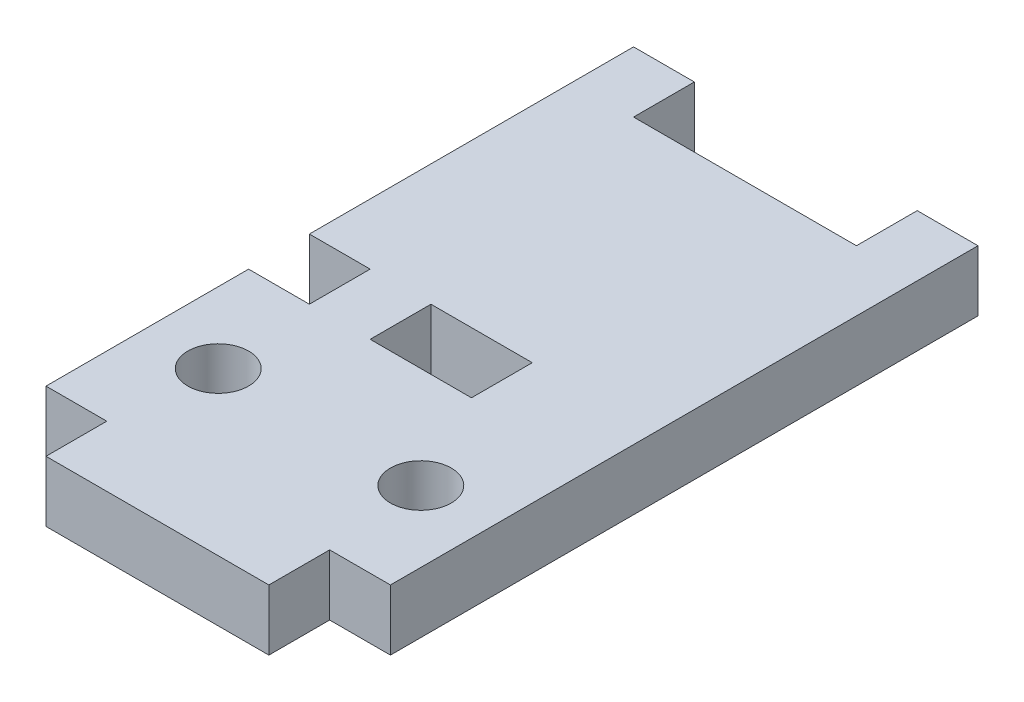
SolidWorks part; units mm, degrees
ref_plane "Plano frontal" through (0, 0, 0) normal (0, 0, 1) x (1, 0, 0)
ref_plane "Plano superior" through (0, 0, 0) normal (0, 1, 0) x (1, 0, 0)
ref_plane "Plano direito" through (0, 0, 0) normal (1, 0, 0) x (0, 0, -1)
sketch "Sketch1" plane through (0, 0, 0) normal (0, 1, 0) x (1, 0, 0)
  line L1 (-8.5, 14.5) -> (8.5, 14.5)
  line L2 (-8.5, 14.5) -> (-8.5, -14.5)
  line L3 (-8.5, -14.5) -> (8.5, -14.5)
  line L4 (8.5, 14.5) -> (8.5, -14.5)
  point P4 (0, 14.5)
  point P6 (-8.5, 0)
  dimension "D1" = 29
  dimension "D2" = 17
extrude "Boss-Extrude1" add sketch "Sketch1" along normal mid plane 3
sketch "Sketch2" plane through (0, 0, 0) normal (0, 1, 0) x (1, 0, 0)
  line L0 (-8.5, -14.5) -> (8.5, -14.5) construction
  line L1 (-5.5, -14.5) -> (5.5, -14.5)
  line L2 (-5.5, -14.5) -> (-5.5, -17.5)
  line L3 (-5.5, -17.5) -> (5.5, -17.5)
  line L4 (5.5, -14.5) -> (5.5, -17.5)
  line L8 (8.5, -14.5) -> (8.5, 14.5) construction
  point P6 (0, -14.5)
  dimension "D1" = 3
  dimension "D3" = 11
  dimension "D4" = 3
extrude "Boss-Extrude2" add sketch "Sketch2" along normal mid plane 3
sketch "Sketch3" plane through (0, 0, 0) normal (0, 1, 0) x (1, 0, 0)
  line L1 (-2.5, -1.5) -> (2.5, -1.5)
  line L2 (-2.5, -1.5) -> (-2.5, -4.5)
  line L3 (-2.5, -4.5) -> (2.5, -4.5)
  line L4 (2.5, -1.5) -> (2.5, -4.5)
  line L5 (-8.5, -14.5) -> (-5.5, -14.5) construction
  line L6 (-5.5, 14.5) -> (5.5, 14.5)
  line L7 (-5.5, 14.5) -> (-5.5, 11.5)
  line L8 (-5.5, 11.5) -> (5.5, 11.5)
  line L9 (5.5, 14.5) -> (5.5, 11.5)
  line L10 (-8.5, -1.5) -> (-5.5, -1.5)
  line L11 (-8.5, 14.5) -> (-8.5, -14.5) construction
  line L12 (8.5, 14.5) -> (-8.5, 14.5) construction
  line L13 (-8.5, -1.5) -> (-8.5, -4.5)
  line L14 (-8.5, -4.5) -> (-5.5, -4.5)
  line L15 (-5.5, -1.5) -> (-5.5, -4.5)
  point P6 (0, -1.5)
  point P12 (0, 11.5)
  dimension "D1" = 3
  dimension "D2" = 10
  dimension "D3" = 5
  dimension "D5" = 3
  dimension "D6" = 11
  dimension "D7" = 3
  dimension "D8" = 3
extrude "Cut-Extrude1" cut sketch "Sketch3" against normal through all both and the other way through all
sketch "Sketch5" plane through (0, 0, 0) normal (0, 1, 0) x (1, 0, 0)
  line L1 (-8.5, -4.5) -> (-5.5, -4.5) construction
  line L2 (-8.5, -14.5) -> (-5.5, -14.5) construction
  line L4 (-8.5, -4.5) -> (-8.5, -14.5) construction
  line L7 (0, -1.65) -> (0, 1.65) construction
  circle A0 centre (-5, -9.5) radius 1.5
  circle A1 centre (5, -9.5) radius 1.5
  dimension "D1" = 3
  dimension "D2" = 3.5
  dimension "D3" = 2
  dimension "D4" = 3.5
extrude "Cut-Extrude3" cut sketch "Sketch5" against normal through all both and the other way through all
